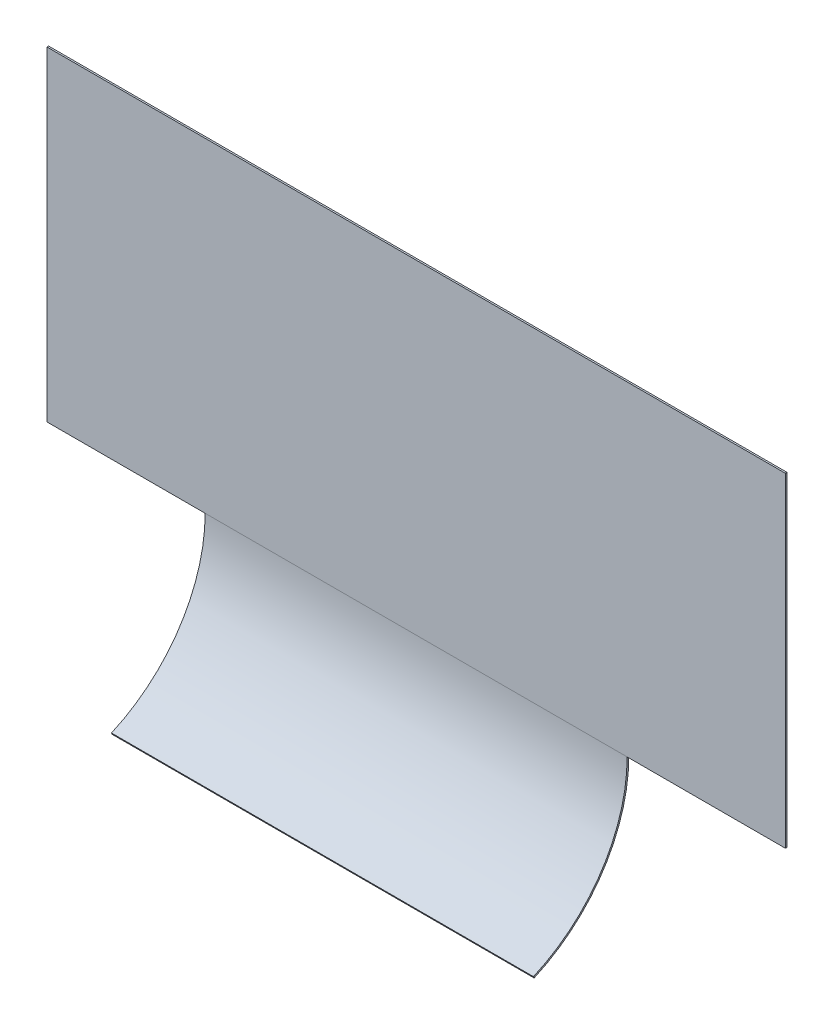
SolidWorks part; units mm, degrees
ref_plane "Front Plane" through (0, 0, 0) normal (0, 0, 1) x (1, 0, 0)
ref_plane "Top Plane" through (0, 0, 0) normal (0, 1, 0) x (1, 0, 0)
ref_plane "Right Plane" through (0, 0, 0) normal (1, 0, 0) x (0, 0, -1)
sketch "Sketch1" plane through (0, 0, 0) normal (1, 0, 0) x (0, 0, -1)
  line L0 (122.7013, -150.8125) -> (-107.8555, -150.8125) construction
  line L1 (150.8125, 0) -> (150.8125, 312.7375)
  arc A0 (60.5751, -138.1125) -> (150.8125, 0) centre (0, 0) ccw
  circle A1 centre (-200.147, -30.0457) radius 63.5 construction
  circle A2 centre (0, 0) radius 36.5125 construction
  dimension "D1" = 12.7
  dimension "D2" = 73.025
  dimension "D3" = 114.3
  dimension "D5" = 127
  dimension "D4" = 349.25
extrude "Extrude-Thin1" add sketch "Sketch1" along normal mid plane 406.4 thin
sketch "Sketch2" plane through (0, 0, -150.8125) normal (0, 0, 1) x (1, 0, 0)
  line L0 (203.2, 312.7375) -> (-203.2, 312.7375) construction
  line L1 (-355.6, 312.7375) -> (355.6, 312.7375)
  line L2 (-355.6, 312.7375) -> (-355.6, 0)
  line L3 (-355.6, 0) -> (355.6, 0)
  line L4 (355.6, 312.7375) -> (355.6, 0)
  line L6 (203.2, 0) -> (-203.2, 0) construction
  dimension "D1" = 711.2
extrude "Boss-Extrude1" add sketch "Sketch2" against normal blind 1.5875
